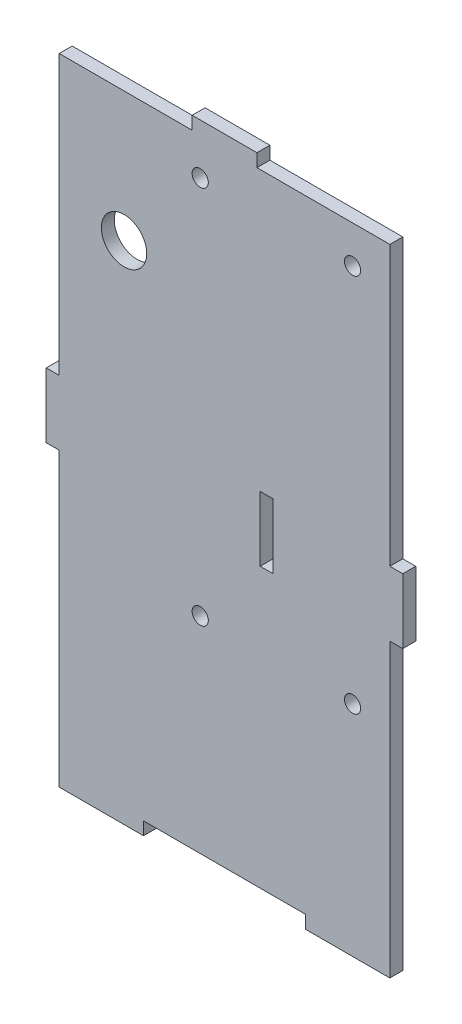
SolidWorks part; units mm, degrees
ref_plane "Front Plane" through (0, 0, 0) normal (0, 0, 1) x (1, 0, 0)
ref_plane "Top Plane" through (0, 0, 0) normal (0, 1, 0) x (1, 0, 0)
ref_plane "Right Plane" through (0, 0, 0) normal (1, 0, 0) x (0, 0, -1)
sketch "Sketch1" plane through (0, 0, 0) normal (0, 0, 1) x (1, 0, 0)
  line L0 (22.5, 100) -> (22.5, 98)
  line L1 (0, 0) -> (55, 0) construction
  line L2 (0, 0) -> (0, 100) construction
  line L3 (0, 100) -> (55, 100) construction
  line L4 (55, 0) -> (55, 100) construction
  line L5 (22.5, 98) -> (2, 98)
  line L6 (2, 98) -> (2, 55)
  line L7 (2, 55) -> (0, 55)
  line L8 (0, 55) -> (0, 45)
  line L9 (0, 45) -> (2, 45)
  line L10 (2, 45) -> (2, 0)
  line L11 (22.5, 100) -> (32.5, 100)
  line L12 (32.5, 100) -> (32.5, 98)
  line L13 (32.5, 98) -> (53, 98)
  line L14 (53, 98) -> (53, 55)
  line L15 (53, 55) -> (55, 55)
  line L16 (55, 55) -> (55, 45)
  line L17 (55, 45) -> (53, 45)
  line L18 (53, 45) -> (53, 0)
  line L19 (53, 0) -> (40, 0)
  line L20 (40, 0) -> (40, 2)
  line L21 (40, 2) -> (15, 2)
  line L22 (15, 2) -> (15, 0)
  line L23 (15, 0) -> (2, 0)
  line L24 (0, 50) -> (55, 50) construction
  line L25 (53, 55) -> (34, 55) construction
  line L26 (34, 55) -> (2, 55) construction
  line L27 (35.5, 95.5) -> (35.5, 30.5) construction
  line L28 (35, 55) -> (33, 55)
  line L29 (35, 55) -> (35, 45)
  line L30 (35, 45) -> (33, 45)
  line L31 (33, 55) -> (33, 45)
  line L32 (50.5, 95.5) -> (20.5, 95.5) construction
  line L33 (50.5, 95.5) -> (50.5, 30.5) construction
  line L34 (50.5, 30.5) -> (20.5, 30.5) construction
  line L35 (20.5, 95.5) -> (20.5, 30.5) construction
  line L36 (20.5, 63) -> (50.5, 63) construction
  line L37 (50.5, 93.5) -> (20.5, 93.5) construction
  line L38 (48.5, 95.5) -> (48.5, 30.5) construction
  circle A0 centre (47.25, 92.25) radius 1.25
  circle A1 centre (23.75, 92.25) radius 1.25
  circle A2 centre (47.25, 33.75) radius 1.25
  circle A3 centre (23.75, 33.75) radius 1.25
  circle A4 centre (12, 78) radius 3.5
  point P25 (0, 50)
  dimension "D13" = 2.5
  dimension "D15" = 2
  dimension "D16" = 7
  dimension "D1" = 55
  dimension "D2" = 100
  dimension "D3" = 10
  dimension "D4" = 2
  dimension "D5" = 25
  dimension "D6" = 50
  dimension "D7" = 18
  dimension "D8" = 2
  dimension "D9" = 30
  dimension "D10" = 65
  dimension "D11" = 5
  dimension "D12" = 5
  dimension "D14" = 2
  dimension "D17" = 10
  dimension "D18" = 20
extrude "Boss-Extrude1" add sketch "Sketch1" along normal blind 2
